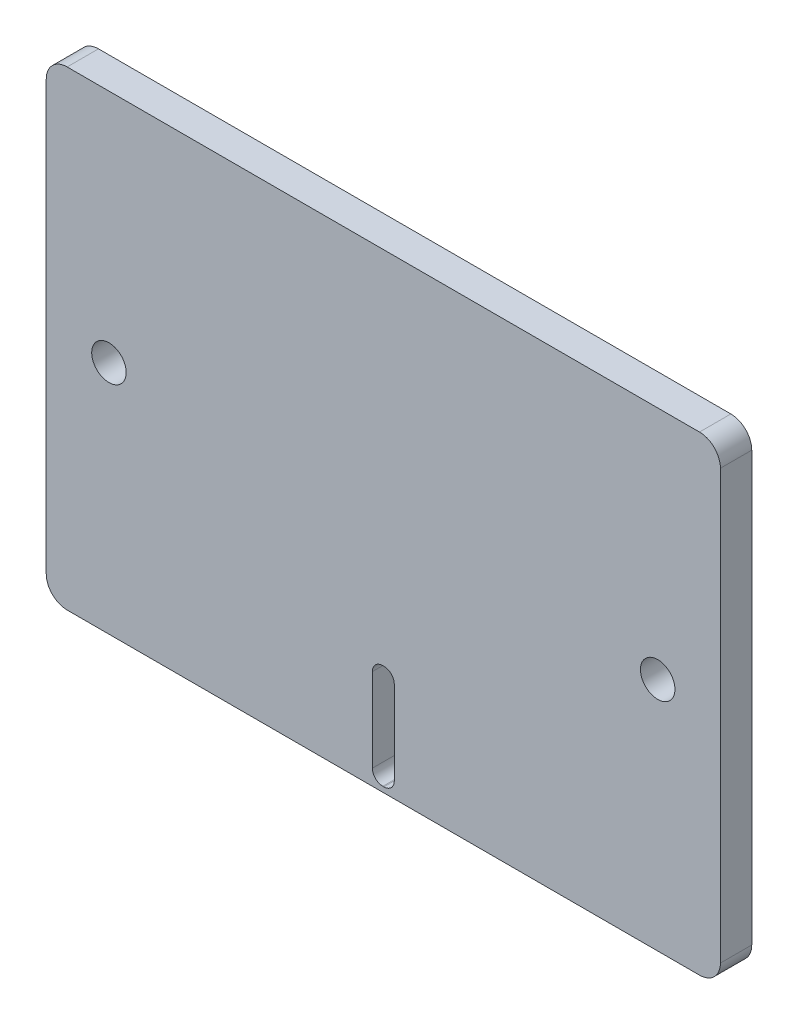
SolidWorks part; units mm, degrees
material "玻璃"
ref_plane "前视基准面" through (0, 0, 0) normal (0, 0, 1) x (1, 0, 0)
ref_plane "上视基准面" through (0, 0, 0) normal (0, 1, 0) x (1, 0, 0)
ref_plane "右视基准面" through (0, 0, 0) normal (1, 0, 0) x (0, 0, -1)
sketch "草图1" plane through (0, 0, 0) normal (0, 0, 1) x (1, 0, 0)
  line L1 (-32.25, -22.5) -> (32.25, -22.5)
  line L2 (-32.25, -22.5) -> (-32.25, 22.5)
  line L3 (-32.25, 22.5) -> (32.25, 22.5)
  line L4 (32.25, -22.5) -> (32.25, 22.5)
  line L5 (-32.25, -22.5) -> (32.25, 22.5) construction
  line L6 (-32.25, 22.5) -> (32.25, -22.5) construction
  point P0 (0, 0)
  dimension "D1" = 64.5
  dimension "D2" = 45
extrude "凸台-拉伸1" add sketch "草图1" along normal blind 3
sketch "草图6" plane through (0, 0, 3) normal (0, 0, 1) x (1, 0, 0)
  line L0 (32.25, -22.5) -> (32.25, 22.5) construction
  line L1 (26.25, -5) -> (38.25, -5)
  line L2 (26.25, -5) -> (26.25, 5)
  line L3 (26.25, 5) -> (38.25, 5)
  line L4 (38.25, -5) -> (38.25, 5)
  line L5 (26.25, -5) -> (38.25, 5) construction
  line L6 (26.25, 5) -> (38.25, -5) construction
  line L7 (0, 0) -> (0, 24.4085) construction
  line L8 (-26.25, 5) -> (-38.25, -5) construction
  line L9 (-26.25, -5) -> (-38.25, 5) construction
  line L10 (-38.25, -5) -> (-38.25, 5)
  line L11 (-26.25, 5) -> (-38.25, 5)
  line L12 (-26.25, -5) -> (-26.25, 5)
  line L13 (-26.25, -5) -> (-38.25, -5)
  point P0 (32.25, 0)
  point P14 (-32.25, 0)
  dimension "D1" = 6
  dimension "D2" = 10
extrude "凸台-拉伸4" add sketch "草图6" against normal up to surface (3 mm away) up to face at (0, 0, 0)
fillet "圆角1" radius 2 12 edges at (-32.25, 22.5, 1.5) (32.25, 22.5, 1.5) (32.25, 5, 1.5) (38.25, 5, 1.5) (38.25, -5, 1.5) (32.25, -5, 1.5) (32.25, -22.5, 1.5) (-32.25, -22.5, 1.5) (-38.25, -5, 1.5) (-38.25, 5, 1.5) (-32.25, -5, 1.5) (-32.25, 5, 1.5)
sketch "草图7" plane through (0, 0, 3) normal (0, 0, 1) x (1, 0, 0)
  line L0 (-35.25, 5) -> (-35.25, -5) construction
  line L1 (-34.25, 5) -> (-36.25, 5) construction
  line L2 (-36.25, -5) -> (-34.25, -5) construction
  line L3 (0, 0) -> (0, 44.1658) construction
  line L4 (35.25, 5) -> (35.25, -5) construction
  circle A0 centre (-35.25, 0) radius 1.65
  circle A1 centre (35.25, 0) radius 1.65
  dimension "D1" = 3.3
extrude "切除-拉伸3" cut sketch "草图7" against normal blind 6
sketch "草图8" plane through (0, 0, 3) normal (0, 0, 1) x (1, 0, 0)
  line L0 (-26.25, 0) -> (0, 0) construction
  line L2 (0, 0) -> (0, -34.1184) construction
  circle A0 centre (-26.25, 0) radius 1.65
  circle A1 centre (-35.25, 0) radius 1.65 construction
  circle A3 centre (26.25, 0) radius 1.65
  dimension "D1" = 26.25
sketch "草图9" plane through (0, 0, 3) normal (0, 0, 1) x (1, 0, 0)
  line L0 (-38.25, 3) -> (-38.25, -3) construction
  line L1 (-32.25, 7) -> (-38.25, 7)
  line L2 (-32.25, 7) -> (-32.25, -7)
  line L3 (-32.25, -7) -> (-38.25, -7)
  line L4 (-38.25, 7) -> (-38.25, -7)
  line L5 (0, 0) -> (0, 36.3262) construction
  line L6 (38.25, 7) -> (38.25, -7)
  line L7 (32.25, -7) -> (38.25, -7)
  line L8 (32.25, 7) -> (32.25, -7)
  line L9 (32.25, 7) -> (38.25, 7)
extrude "切除-拉伸4" cut sketch "草图9" against normal blind 10
extrude "切除-拉伸5" cut sketch "草图8" against normal blind 10
sketch "草图10" plane through (0, 0, 3) normal (0, 0, 1) x (1, 0, 0)
  line L0 (0, 0) -> (0, -17) construction
  line L2 (-1.05, -12) -> (1.05, -12)
  line L3 (-1.05, -12) -> (-1.05, -22)
  line L4 (-1.05, -22) -> (1.05, -22)
  line L5 (1.05, -12) -> (1.05, -22)
  line L6 (-1.05, -12) -> (1.05, -22) construction
  line L7 (-1.05, -22) -> (1.05, -12) construction
  dimension "D1" = 2.1
  dimension "D2" = 10
  dimension "D3" = 17
extrude "切除-拉伸6" cut sketch "草图10" against normal blind 10
fillet "圆角2" radius 1 4 edges at (1.05, -22, 1.5) (-1.05, -22, 1.5) (-1.05, -12, 1.5) (1.05, -12, 1.5)
